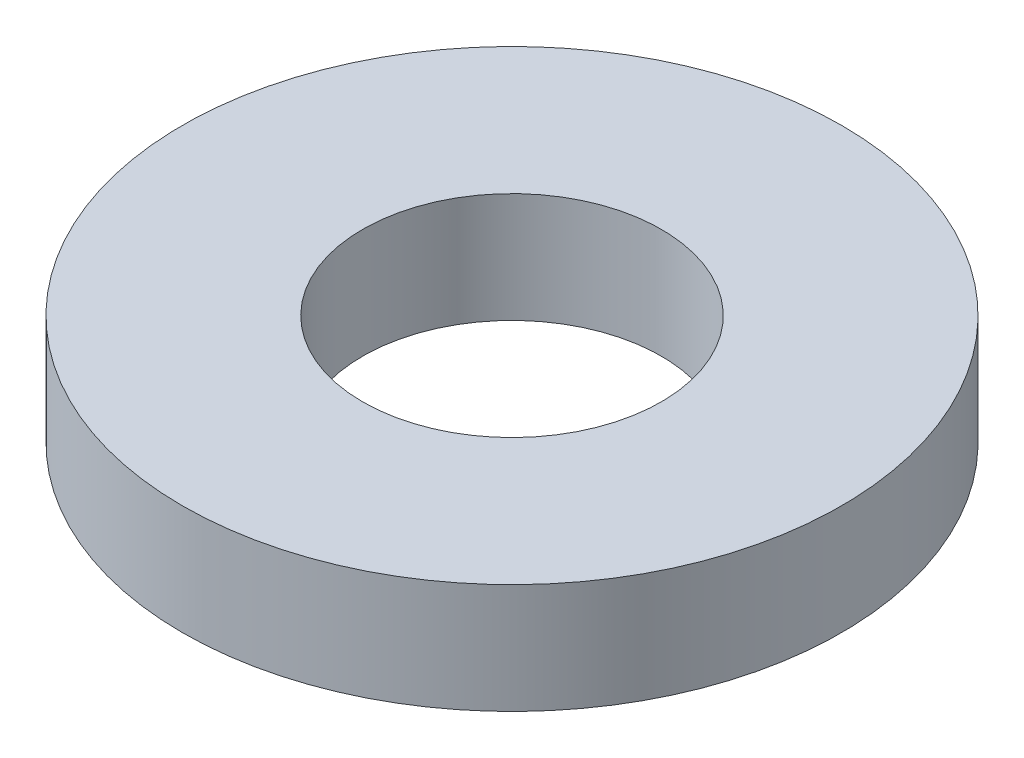
SolidWorks part; units mm, degrees
material "Nylon 6/10"
ref_plane "Front Plane" through (0, 0, 0) normal (0, 0, 1) x (1, 0, 0)
ref_plane "Top Plane" through (0, 0, 0) normal (0, 1, 0) x (1, 0, 0)
ref_plane "Right Plane" through (0, 0, 0) normal (1, 0, 0) x (0, 0, -1)
sketch "Sketch1" plane through (0, 0, 0) normal (0, 1, 0) x (1, 0, 0)
  circle A0 centre (0, 0) radius 2.159
  circle A1 centre (0, 0) radius 4.7625
  dimension "D1" = 4.318
  dimension "D2" = 9.525
extrude "Boss-Extrude1" add sketch "Sketch1" along normal blind 1.5875
